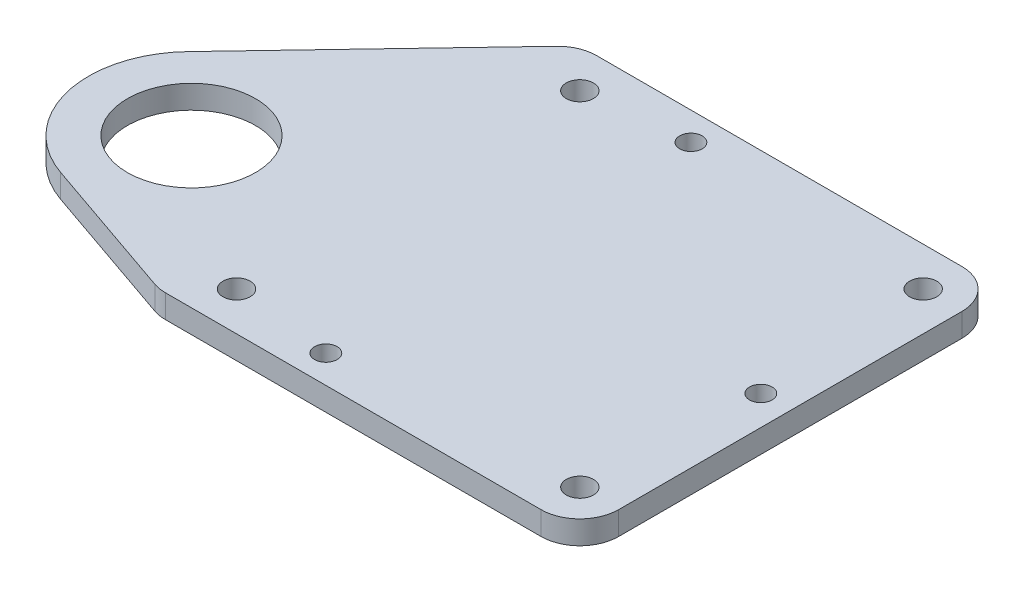
SolidWorks part; units mm, degrees
ref_plane "Front Plane" through (0, 0, 0) normal (0, 0, 1) x (1, 0, 0)
ref_plane "Top Plane" through (0, 0, 0) normal (0, 1, 0) x (1, 0, 0)
ref_plane "Right Plane" through (0, 0, 0) normal (1, 0, 0) x (0, 0, -1)
sketch "Sketch1" plane through (0, 0, 0) normal (0, 1, 0) x (1, 0, 0)
  line L0 (17.9, 50.6) -> (17.9, 3.6) construction
  line L1 (0, 0) -> (54.2, 0)
  line L2 (0, 0) -> (0, 54.2)
  line L3 (0, 54.2) -> (54.2, 54.2)
  line L4 (54.2, 0) -> (54.2, 54.2)
  line L5 (17.9, 27.1) -> (50.4, 27.1) construction
  line L6 (0, 54.2) -> (17.9, 50.6) construction
  line L7 (0, 0) -> (17.9, 3.6) construction
  line L8 (5, 49.2) -> (0, 54.2) construction
  line L9 (5, 49.2) -> (49.2, 49.2) construction
  line L10 (5, 49.2) -> (5, 5) construction
  line L11 (5, 5) -> (49.2, 5) construction
  line L12 (49.2, 49.2) -> (49.2, 5) construction
  line L13 (49.2, 49.2) -> (54.2, 54.2) construction
  line L14 (49.2, 5) -> (54.2, 0) construction
  line L15 (5, 5) -> (0, 0) construction
  line L16 (0, 0) -> (-19.3263, 6.6762)
  line L18 (0, 54.2) -> (-24.6014, 28.331)
  circle A0 centre (17.9, 50.6) radius 1.45
  circle A1 centre (17.9, 3.6) radius 1.45
  circle A2 centre (50.4, 27.1) radius 1.45
  circle A3 centre (5, 49.2) radius 1.75
  circle A4 centre (49.2, 49.2) radius 1.75
  circle A5 centre (49.2, 5) radius 1.75
  circle A6 centre (5, 5) radius 1.75
  circle A7 centre (-15, 19.2) radius 8.25
  circle A8 centre (-15, 19.2) radius 13.25
  point P25 (-15, 36.4022)
  dimension "D1" = 47
  dimension "D4" = 2.9
  dimension "D7" = 3.5
  dimension "D9" = 16.5
  dimension "D10" = 26.5
  dimension "D2" = 32.5
  dimension "D3" = 54.2
  dimension "D5" = 54.2
  dimension "D6" = 3.8
  dimension "D8" = 5
  dimension "D11" = 15
  dimension "D12" = 35
extrude "Boss-Extrude1" add sketch "Sketch1" along normal blind 3 contours L1 L4 L3 L2 A6 A5 A4 A3 A2 A1 A0 | A8 L16 L2 L18 | A8 A7
fillet "Fillet1" radius 5 4 edges at (54.2, 1.5, -54.2) (54.2, 1.5, 0) (0, 1.5, 0) (0, 1.5, -54.2)
